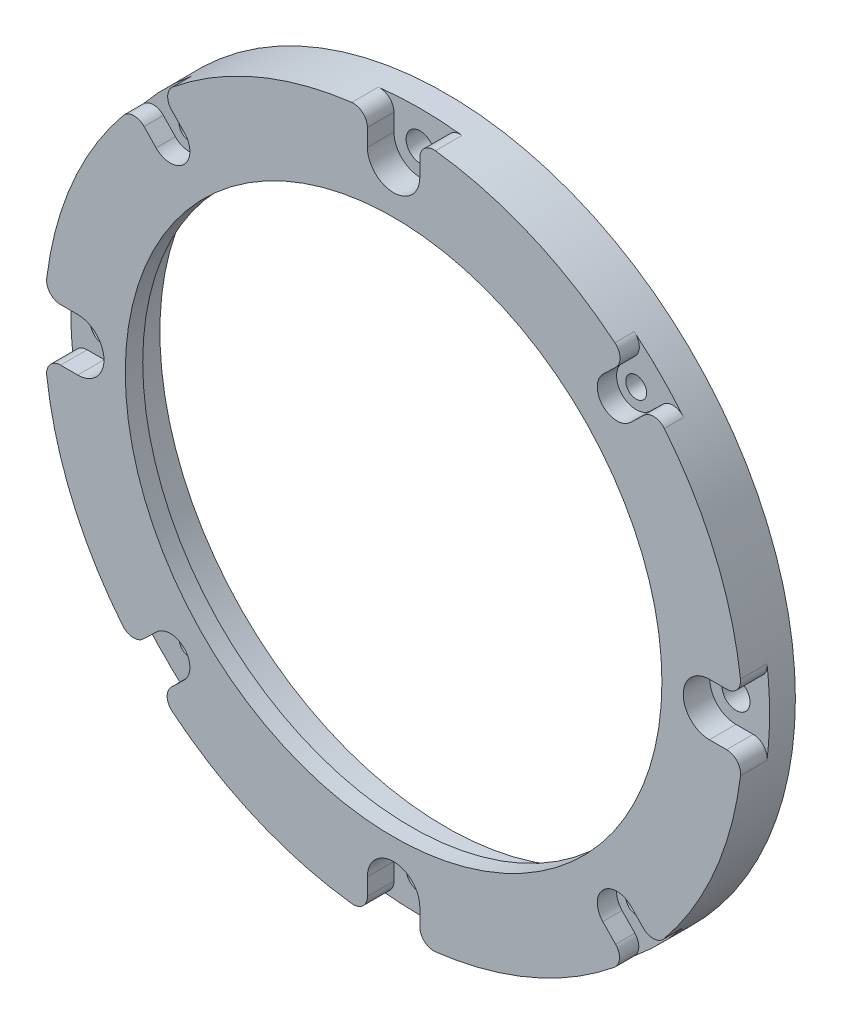
SolidWorks part; units mm, degrees
material "6061-T6 (SS)"
ref_plane "Front Plane" through (0, 0, 0) normal (0, 0, 1) x (1, 0, 0)
ref_plane "Top Plane" through (0, 0, 0) normal (0, 1, 0) x (1, 0, 0)
ref_plane "Right Plane" through (0, 0, 0) normal (1, 0, 0) x (0, 0, -1)
sketch "Sketch1" plane through (0, 0, 0) normal (0, 1, 0) x (1, 0, 0)
  line L0 (0, 0) -> (63.5, 0)
  line L1 (63.5, 0) -> (63.5, -9.525)
  line L2 (63.5, -9.525) -> (48.768, -9.525)
  line L3 (48.768, -9.525) -> (48.768, -6.35)
  line L4 (48.768, -6.35) -> (0, -6.35)
  line L5 (0, -6.35) -> (0, 0)
  dimension "D1" = 6.35
  dimension "D2" = 3.175
  dimension "D3" = 63.5
  dimension "D4" = 48.768
revolve "Revolve1" add sketch "Sketch1" angle 360 about L5
sketch "Sketch2" plane through (0, 0, 6.35) normal (0, 0, 1) x (1, 0, 0)
  circle A0 centre (0, 0) radius 52
  dimension "D1" = 104
extrude "Cut-Extrude1" cut sketch "Sketch2" against normal through all
hole_wizard "CBORE for #6 Socket Head Cap Screw1" positions "Sketch4" profile "Sketch5" counterbore size "#6" standard "ANSI Inch" end condition through all
sketch "Sketch4" plane through (41.7483, 9.0893, 9.525) normal (0, 0, -1) x (-1, 0, 0)
  line L0 (24.6228, -9.0893) -> (67.1822, -9.0893) construction
  line L2 (41.7483, -9.0893) -> (58.8104, 7.9729) construction
  point P0 (82.3391, 31.5015)
  dimension "D1" = 45
  dimension "D2" = 57.404
sketch "Sketch5" plane through (-40.5908, 40.5908, 9.525) normal (1, 0, 0) x (0, -1, 0)
  line L0 (0, 0) -> (0, 9.525)
  line L1 (0, 9.525) -> (1.8986, 9.525)
  line L3 (1.8986, 9.525) -> (1.8986, 3.5052)
  line L4 (1.8986, 3.5052) -> (3.5725, 3.5052)
  line L5 (3.5725, 3.5052) -> (3.5725, 0)
  line L7 (3.5725, 0) -> (0, 0)
  line L11 (0, -6.35) -> (0, 107.95) construction
  dimension "Thru Hole Dia." = 3.7973
  dimension "Thru Hole Depth" = 9.525
  dimension "C'Bore Dia." = 7.145
  dimension "C'Bore Depth" = 3.5052
sketch "Sketch15" plane through (0, 0, 9.525) normal (0, 0, 1) x (1, 0, 0)
  line L0 (-43.1636, 38.1122) -> (-38.0179, 43.0694)
  line L1 (-43.1636, 38.1122) -> (-47.3999, 42.5095)
  line L2 (-38.0179, 43.0694) -> (-42.2543, 47.4667)
  line L3 (-47.3999, 42.5095) -> (-42.2543, 47.4667)
  circle A0 centre (-40.5908, 40.5908) radius 3.5725 construction
  circle A1 centre (-40.5908, 40.5908) radius 3.5725 construction
  circle A2 centre (0, 0) radius 63.5 construction
extrude "Cut-Extrude3" cut sketch "Sketch15" against normal up to surface (3.5052 mm away) up to face at (-38.6921, 40.5908, 6.0198)
fillet "Fillet2" radius 2.54 2 edges at (-47.282, 42.3871, 7.7724) (-42.22, 47.4312, 7.7724)
pattern_circular "CirPattern1" count 4 over 360 about axis through (0, 0, 0) along (0, 0, 1) of "CBORE for #6 Socket Head Cap Screw1", "Fillet2", "Cut-Extrude3"
hole_wizard "CBORE for #10 Socket Head Cap Screw1" positions "Sketch11" profile "Sketch10" counterbore size "#10" standard "ANSI Inch" end condition through all
sketch "Sketch11" plane through (0, 0, 9.525) normal (0, 0, 1) x (1, 0, 0)
  line L0 (0, 0) -> (0, 50000) construction
  point P0 (0, 57.404)
  dimension "D1" = 57.404
sketch "Sketch10" plane through (0, 57.404, 9.525) normal (1, 0, 0) x (0, -1, 0)
  line L0 (0, 0) -> (0, 9.525)
  line L1 (0, 9.525) -> (2.5527, 9.525)
  line L3 (2.5527, 9.525) -> (2.5527, 4.826)
  line L4 (2.5527, 4.826) -> (4.7625, 4.826)
  line L5 (4.7625, 4.826) -> (4.7625, 0)
  line L7 (4.7625, 0) -> (0, 0)
  line L11 (0, -6.35) -> (0, 107.95) construction
  dimension "Thru Hole Dia." = 5.1054
  dimension "Thru Hole Depth" = 9.525
  dimension "C'Bore Dia." = 9.525
  dimension "C'Bore Depth" = 4.826
sketch "Sketch12" plane through (0, 0, 9.525) normal (0, 0, 1) x (1, 0, 0)
  line L0 (-4.7625, 57.404) -> (-4.7625, 63.5)
  line L1 (-4.7625, 63.5) -> (4.7625, 63.5)
  line L2 (4.7625, 63.5) -> (4.7625, 57.404)
  line L3 (4.7625, 57.404) -> (-4.7625, 57.404)
  circle A0 centre (0, 57.404) radius 4.7625 construction
  circle A1 centre (0, 57.404) radius 4.7625 construction
  circle A2 centre (0, 0) radius 63.5 construction
extrude "Cut-Extrude2" cut sketch "Sketch12" against normal up to surface (4.826 mm away) up to face at (2.5527, 57.404, 4.699)
fillet "Fillet1" radius 2.54 2 edges at (4.7625, 63.3212, 7.112) (-4.7625, 63.3212, 7.112)
pattern_circular "CirPattern2" count 4 over 360 about axis through (0, 0, 0) along (0, 0, 1) of "CBORE for #10 Socket Head Cap Screw1", "Cut-Extrude2", "Fillet1"
sketch "Sketch14" plane through (0, 0, 9.525) normal (0, 0, 1) x (1, 0, 0)
  text T0 "AUVic                    AUVic         " font "Century Gothic" height in points 26
extrude "Boss-Extrude1" [suppressed] add sketch "Sketch14" along normal blind 2.54
